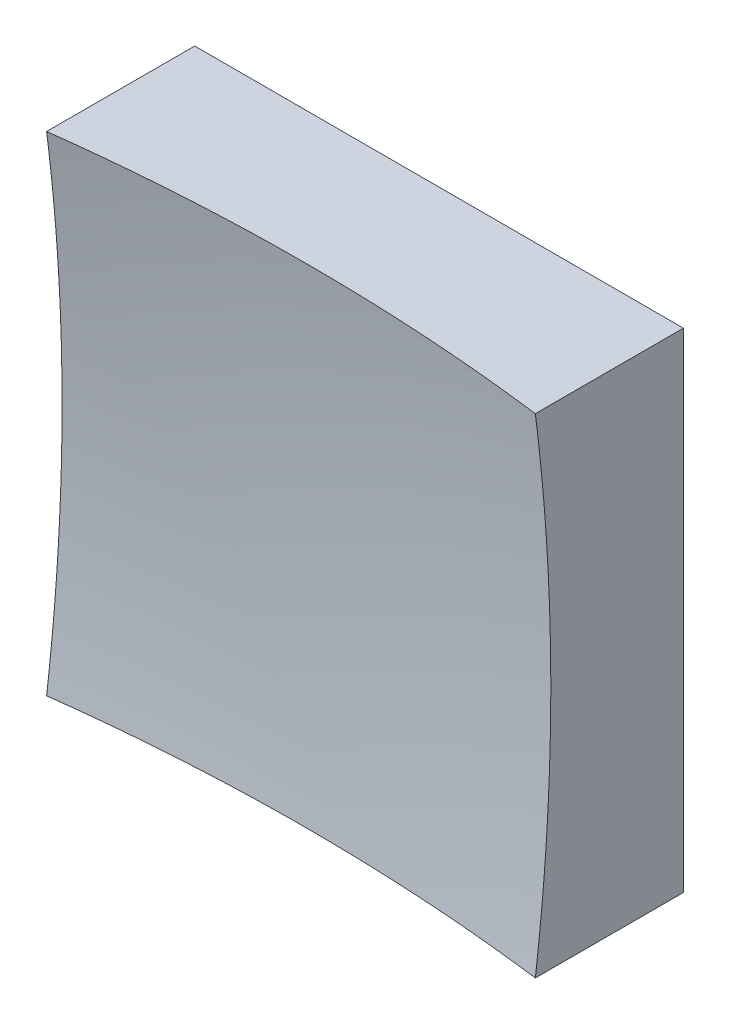
SolidWorks part; units mm, degrees
ref_plane "前视基准面" through (0, 0, 0) normal (0, 0, 1) x (1, 0, 0)
ref_plane "上视基准面" through (0, 0, 0) normal (0, 1, 0) x (1, 0, 0)
ref_plane "右视基准面" through (0, 0, 0) normal (1, 0, 0) x (0, 0, -1)
sketch "草图1" plane through (0, 0, 0) normal (0, 0, 1) x (1, 0, 0)
  line L1 (-12.5, 12.5) -> (12.5, 12.5)
  line L2 (-12.5, 12.5) -> (-12.5, -12.5)
  line L3 (-12.5, -12.5) -> (12.5, -12.5)
  line L4 (12.5, 12.5) -> (12.5, -12.5)
  line L5 (-12.5, 12.5) -> (12.5, -12.5) construction
  line L6 (-12.5, -12.5) -> (12.5, 12.5) construction
  point P0 (0, 0)
  dimension "D1" = 25
  dimension "D2" = 25
extrude "凸台-拉伸1" add sketch "草图1" along normal blind 20 contours L2 L3 L4 L1
sketch "草图2" plane through (0, 0, 0) normal (0, 1, 0) x (1, 0, 0)
  line L0 (-7.4603, -6) -> (7.3192, -6) construction
  line L1 (0, 0) -> (0, -12.1749) construction
  line L2 (97.4845, -83.7118) -> (0, -83.7118)
  line L3 (0, -83.7118) -> (0, -6)
  arc A1 (97.4845, -83.7118) -> (0, -6) centre (0, -106) ccw
  dimension "D2" = 200
  dimension "D1" = 6
revolve "切除-旋转2" cut sketch "草图2" angle 360 about L3
